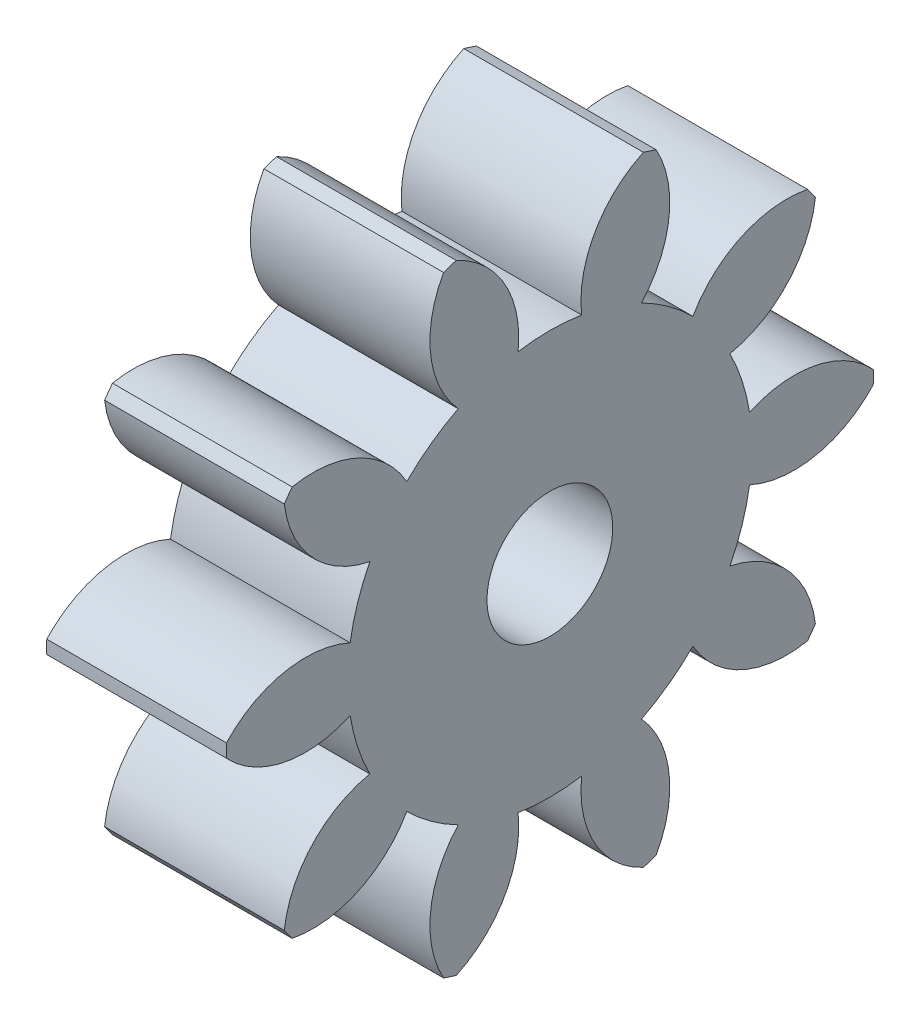
SolidWorks part; units mm, degrees
ref_plane "Plane1" through (0, 0, 0) normal (0, 0, 1) x (1, 0, 0)
ref_plane "Plane2" through (0, 0, 0) normal (0, 1, 0) x (1, 0, 0)
ref_plane "Plane3" through (0, 0, 0) normal (1, 0, 0) x (0, 0, -1)
sketch "HoldingSke" plane through (0, 0, 0) normal (0, 1, 0) x (1, 0, 0)
  line L0 (0, 0) -> (0.3283, -0.0579)
  line L1 (-15, 0) -> (100, 0) construction
  line L2 (0, 0) -> (-2.1039, 2.3779)
  line L3 (0, 0) -> (-11.863, 4.5341)
  line L4 (0, 0) -> (8.5048, 1.4996)
  line L5 (0, 0) -> (-46.8476, -17.4728)
  line L6 (0, 0) -> (-8.2896, -5.593)
  line L7 (-2.1039, 2.3779) -> (8.6586, 51.2059)
  line L8 (-76.2, 54.61) -> (-75.2, 54.61)
  line L9 (-71.009, 38.7566) -> (-53.1078, 45.2721)
  line L10 (-76.2, 71.12) -> (104.1128, 71.12)
  line L11 (0, 0) -> (-10, 0)
  line L12 (-76.2, 101.6) -> (-76.093, 101.6)
  line L13 (24.9733, 27.94) -> (52.9518, 28.4284)
  line L14 (24.9733, 27.94) -> (24.9743, 27.94)
  line L15 (24.9733, 27.94) -> (100.4006, 29.5858)
  line L16 (-63.627, -3) -> (-12.827, -3)
  circle A0 centre (0, 0) radius 3.5
  circle A1 centre (0, 0) radius 11.249
  circle A2 centre (0, 0) radius 37.5
  circle A3 centre (0, 0) radius 3.5
  dimension "MHD" = 22.498
  dimension "Hub_dia" = 75
  dimension "Bore" = 7
  dimension "MBD" = 7
  dimension "Num_teeth" = 10
  dimension "Pitch" = 0.3333
  dimension "Overall_len" = 50
  dimension "Show_teeth" = 10
  dimension "Thickness" = 10
  dimension "OAL" = 50.0001
  dimension "T_dim" = 1
  dimension "Ap" = 20
  dimension "H" = 19.05
  dimension "Pitch_radius" = 180.3128
  dimension "Width" = 10
  dimension "Backlash" = 0.107
  dimension "Addendum_fac" = 1
  dimension "Dedendum_fac" = 1.25
  dimension "Clearance_fac" = 0.25
  dimension "Dedendum_add" = 0.001
  dimension "Module" = 3
sketch "BasProSke" plane through (0, 0, 0) normal (0, 1, 0) x (1, 0, 0)
  line L0 (-10, 0) -> (60, 0) construction
  line L1 (0, 0) -> (0, 18)
  line L2 (0, 0) -> (10, 0)
  line L3 (10, 0) -> (10, 18)
  line L4 (10, 18) -> (0, 18)
  dimension "Thickness" = 10
  dimension "Diameter" = 36
revolve "Base-Revolve" add sketch "BasProSke" angle 360 about L0
sketch "TooCutSke" plane through (0, 0, 0) normal (1, 0, 0) x (0, 0, -1)
  line L1 (0, 0) -> (0, 107) construction
  line L2 (0, 0) -> (-2.5334, 14.7845) construction
  line L3 (0, 0) -> (-9.174, 28.2345) construction
  line L4 (-2.5334, 14.7845) -> (-4.587, 14.1173) construction
  arc A0 (1.7689, 11.109) -> (-1.7689, 11.109) centre (0, 0) ccw
  arc A1 (5.2426, 17.2462) -> (-5.2426, 17.2462) centre (0, 0) ccw
  circle A2 centre (0, 0) radius 15 construction
  circle A3 centre (0, 0) radius 14.0954 construction
  arc A4 (-1.7689, 11.109) -> (-5.2426, 17.2462) centre (-7.7306, 11.7863) ccw
  arc A5 (5.2426, 17.2462) -> (1.7689, 11.109) centre (7.7306, 11.7863) ccw
  dimension "Root_dia" = 22.498
  dimension "Overcut_dia" = 36.0508
  dimension "Pitch_dia" = 30
  dimension "Base_dia" = 28.1908
  dimension "Flank_rad" = 6
  dimension "Half_ang" = 18
  dimension "Half_CT" = 2.1593
extrude "ToothCut" cut sketch "TooCutSke" along normal through all
fillet "Breaks" [suppressed] radius 0.06
fillet "RootFillets" [suppressed] radius 0.751
pattern_circular "TeethCuts" count 10 every 36 about axis through (-10, 0, 0) along (1, 0, 0) of "ToothCut", "RootFillets", "Breaks"
sketch "HubNeaOneSke" plane through (0, 0, 0) normal (-1, 0, 0) x (0, 0, 1)
  circle A0 centre (0, 0) radius 11.249
  dimension "Diameter" = 22.498
extrude "HubNearOne" [suppressed] add sketch "HubNeaOneSke" along normal blind 40.0001
sketch "HubNeaBotSke" plane through (0, 0, 0) normal (-1, 0, 0) x (0, 0, 1)
  circle A0 centre (0, 0) radius 11.249
  dimension "Diameter" = 22.498
extrude "HubNearBoth" [suppressed] add sketch "HubNeaBotSke" along normal blind 20
ref_plane "FarPln" through (10, 0, 0) normal (1, 0, 0) x (0, 0, -1)
sketch "HubFarSke" plane through (10, 0, 0) normal (1, 0, 0) x (0, 0, -1)
  circle A0 centre (0, 0) radius 11.249
  dimension "Diameter" = 22.498
extrude "HubFar" [suppressed] add sketch "HubFarSke" along normal blind 20
sketch "BorSke" plane through (0, 0, 0) normal (1, 0, 0) x (0, 0, -1)
  circle A0 centre (0, 0) radius 3.5
  dimension "Diameter" = 7
extrude "Bore" cut sketch "BorSke" along normal mid plane 100.0001
sketch "KeySke" plane through (0, 0, 0) normal (1, 0, 0) x (0, 0, -1)
  line L0 (-1, 0) -> (-1, 4.5)
  line L1 (-1, 4.5) -> (1, 4.5)
  line L2 (1, 4.5) -> (1, 0)
  line L3 (0, 0) -> (0, 34) construction
  line L4 (-1, 0) -> (1, 0)
  dimension "Offset" = 4.5
  dimension "Width" = 2
extrude "Keyway" [suppressed] cut sketch "KeySke" along normal mid plane 100.0001
pattern_circular "Keyway2" [suppressed] count 2 every 90 about axis through (-10, 0, 0) along (1, 0, 0)
equation "' \"Module@HoldingSke\" = 6.35"
equation "' \"Num_teeth@HoldingSke\" = 12"
equation "' \"Ap@HoldingSke\" =  20"
equation "' \"Ap@HoldingSke\" = 20"
equation "' \"Width@HoldingSke\" = 0.5 * 25.4"
equation "' \"Hub_dia@HoldingSke\"= 1 * 25.4"
equation "' \"Hub_dia@HoldingSke\" = 1 * 25.4"
equation "' \"Overall_len@HoldingSke\" = 1.0 * 25.4"
equation "' \"Bore@HoldingSke\" = 0.75 * 25.4"
equation "' \"T_dim@HoldingSke\" = 0.1 * 25.4"
equation "' \"Width@KeySke\" = 0.25 * 25.4"
equation "' \"Show_teeth@HoldingSke\" = 13"
equation "' \"Backlash@HoldingSke\" = 0.009 * 25.4"
equation "' \"Addendum_fac@HoldingSke\" = 1.0"
equation "' \"Dedendum_fac@HoldingSke\" = 1.25"
equation "' \"Dedendum_add@HoldingSke\" = 0.00005 * 25.4"
equation "' \"Clearance_fac@HoldingSke\" = 0.25"
equation "\"Pitch@HoldingSke\" = 1 / \"Module@HoldingSke\""
equation "\"Overcut_dia@TooCutSke\" = (\"Num_teeth@HoldingSke\" + 2 * \"Addendum_fac@HoldingSke\") / \"Pitch@HoldingSke\" + 0.002 * 25.4"
equation "\"Pitch_dia@TooCutSke\" = \"Num_teeth@HoldingSke\" / \"Pitch@HoldingSke\""
equation "\"Base_dia@TooCutSke\" = \"Num_teeth@HoldingSke\" / \"Pitch@HoldingSke\" * cos((\"Ap@HoldingSke\"  * 3.14159265 / 180))"
equation "\"Root_dia@TooCutSke\" = (\"Num_teeth@HoldingSke\" + 2) / \"Pitch@HoldingSke\" - 2 * (\"Addendum_fac@HoldingSke\" + \"Dedendum_fac@HoldingSke\") / \"Pitch@HoldingSke\" - \"Dedendum_add@HoldingSke\" * 2"
equation "\"Half_ang@TooCutSke\" = 180 / \"Num_teeth@HoldingSke\""
equation "\"Half_CT@TooCutSke\" = \"Num_teeth@HoldingSke\" / \"Pitch@HoldingSke\" * sin((3.14159265 / 2 / \"Num_teeth@HoldingSke\")) / 2 - 7 * \"Backlash@HoldingSke\" / 4"
equation "\"Flank_rad@TooCutSke\" = \"Num_teeth@HoldingSke\" / \"Pitch@HoldingSke\" / 5"
equation "\"Radius@RootFillets\" = \"Clearance_fac@HoldingSke\" / \"Pitch@HoldingSke\" + \"Dedendum_add@HoldingSke\""
equation "\"Break_rad@Breaks\" = 0.02 / \"Pitch@HoldingSke\""
equation "\"Thickness@HoldingSke\" = \"Width@HoldingSke\""
equation "\"OAL@HoldingSke\" = \"Thickness@HoldingSke\""
equation "\"MHD@HoldingSke\" = (\"Num_teeth@HoldingSke\" + 2) / \"Pitch@HoldingSke\" - 2 * (\"Addendum_fac@HoldingSke\" + \"Dedendum_fac@HoldingSke\")  / \"Pitch@HoldingSke\" - \"Dedendum_add@HoldingSke\" * 2"
equation "\"MBD@HoldingSke\" = (\"Num_teeth@HoldingSke\" + 2) / \"Pitch@HoldingSke\" - 2 * (\"Addendum_fac@HoldingSke\" + \"Dedendum_fac@HoldingSke\")  / \"Pitch@HoldingSke\" - \"Dedendum_add@HoldingSke\" * 2 - 0.002 * 25.4"
equation "\"MHD@HoldingSke\" = ((sgn( \"MHD@HoldingSke\" - \"Hub_dia@HoldingSke\" )-1)*( \"MHD@HoldingSke\" - \"Hub_dia@HoldingSke\" ))/-2+ \"Hub_dia@HoldingSke\""
equation "\"MBD@HoldingSke\" = ((sgn( \"MBD@HoldingSke\" - \"Bore@HoldingSke\" )-1)*( \"MBD@HoldingSke\" - \"Bore@HoldingSke\" ))/-2+ \"Bore@HoldingSke\""
equation "\"OAL@HoldingSke\" = ((sgn( \"OAL@HoldingSke\" - \"Overall_len@HoldingSke\" )+1)*( \"OAL@HoldingSke\" - \"Overall_len@HoldingSke\" ))/2 + \"Overall_len@HoldingSke\" + 0.000002 * 25.4"
equation "\"Num_teeth@TeethCuts\" = int( \"Show_teeth@HoldingSke\" ) + 1"
equation "\"Num_teeth@TeethCuts\" = ((sgn( \"Num_teeth@TeethCuts\" - \"Num_teeth@HoldingSke\" )-1)*( \"Num_teeth@TeethCuts\" - \"Num_teeth@HoldingSke\" ))/-2+ \"Num_teeth@HoldingSke\""
equation "\"Num_teeth@TeethCuts\" = ((sgn( \"Num_teeth@TeethCuts\" - 2.0)+1)*( \"Num_teeth@TeethCuts\" - 2.0))/2 +2.0"
equation "\"Angle@TeethCuts\" = 360.0 / \"Num_teeth@HoldingSke\""
equation "\"Diameter@BasProSke\" = (\"Num_teeth@HoldingSke\" + 2 * \"Addendum_fac@HoldingSke\") / \"Pitch@HoldingSke\""
equation "\"Thickness@BasProSke\"  = \"Thickness@HoldingSke\""
equation "' \"Fillet_rad@BasProSke\" =  \"Thickness@HoldingSke\" * 0.05"
equation "' \"Fillet_rad@BasProSke\" = \"Thickness@HoldingSke\" * 0.05"
equation "\"MHD@HoldingSke\" = ((sgn( \"MHD@HoldingSke\" - \"Root_dia@TooCutSke\" )-1)*( \"MHD@HoldingSke\" - \"Root_dia@TooCutSke\" ))/-2+ \"Root_dia@TooCutSke\""
equation "\"Diameter@HubNeaOneSke\" = \"MHD@HoldingSke\""
equation "\"Length@HubNearOne\" = \"OAL@HoldingSke\" - \"Thickness@BasProSke\""
equation "\"Diameter@HubNeaBotSke\" = \"MHD@HoldingSke\""
equation "\"Length@HubNearBoth\" = ( \"OAL@HoldingSke\" - \"Thickness@BasProSke\" ) / 2.0"
equation "\"Thickness@FarPln\" = \"Thickness@BasProSke\""
equation "\"Diameter@HubFarSke\" = \"MHD@HoldingSke\""
equation "\"Length@HubFar\" = ( \"OAL@HoldingSke\" - \"Thickness@BasProSke\" ) / 2.0"
equation "\"Diameter@BorSke\" = \"MBD@HoldingSke\""
equation "\"D1@Bore\" = \"OAL@HoldingSke\" * 2.0"
equation "\"D1@Keyway\" = \"OAL@HoldingSke\" * 2.0"
equation "\"Offset@KeySke\" = \"T_dim@HoldingSke\" + \"MBD@HoldingSke\" / 2.0"
